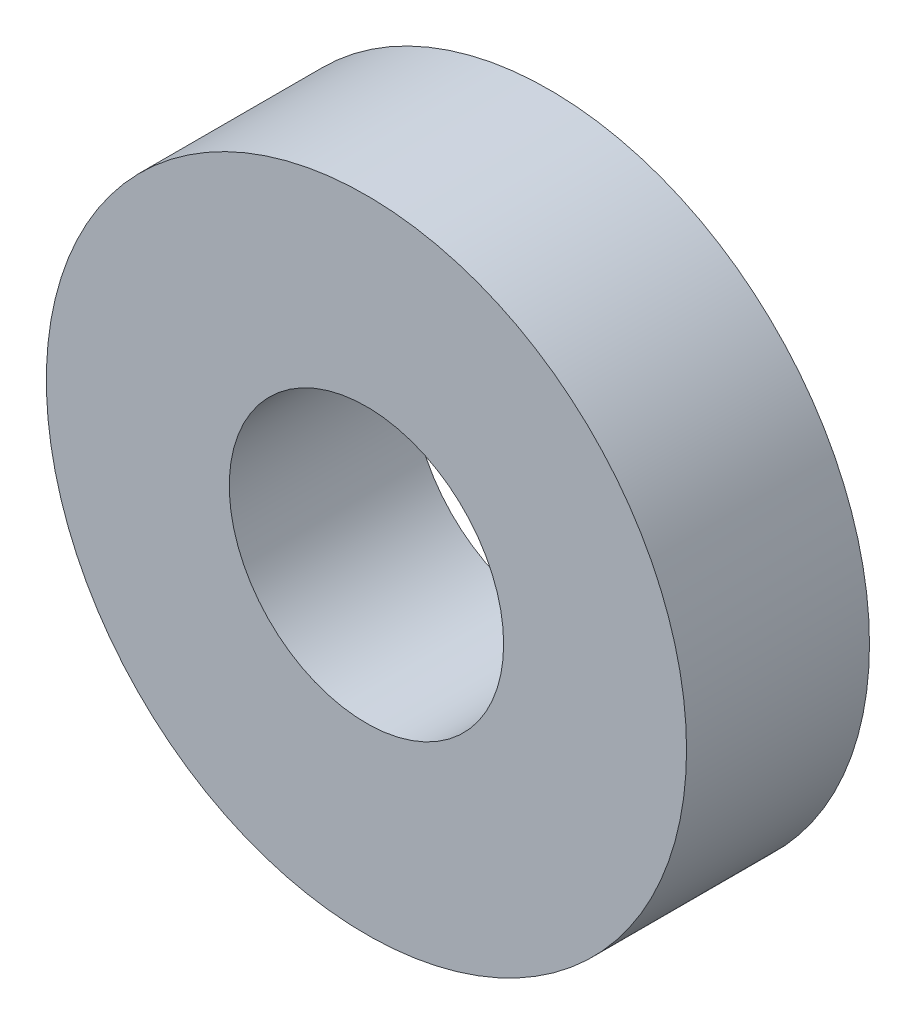
SolidWorks part; units mm, degrees
ref_plane "Front Plane" through (0, 0, 0) normal (0, 0, 1) x (1, 0, 0)
ref_plane "Top Plane" through (0, 0, 0) normal (0, 1, 0) x (1, 0, 0)
ref_plane "Right Plane" through (0, 0, 0) normal (1, 0, 0) x (0, 0, -1)
sketch "Sketch1" plane through (0, 0, 0) normal (0, 0, 1) x (1, 0, 0)
  circle A0 centre (0, 0) radius 0.75
  circle A1 centre (0, 0) radius 1.75
  dimension "D1" = 1.5
  dimension "D2" = 3.5
extrude "Boss-Extrude1" add sketch "Sketch1" along normal blind 1
